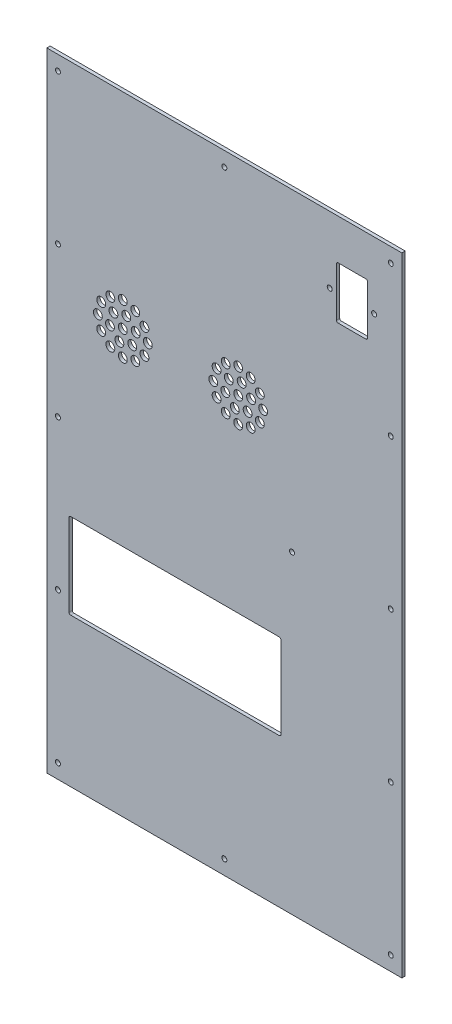
SolidWorks part; units mm, degrees
ref_plane "Спереди" through (0, 0, 0) normal (0, 0, 1) x (1, 0, 0)
ref_plane "Сверху" through (0, 0, 0) normal (0, 1, 0) x (1, 0, 0)
ref_plane "Справа" through (0, 0, 0) normal (1, 0, 0) x (0, 0, -1)
sketch "Эскиз1" plane through (0, 0, 0) normal (0, 0, 1) x (1, 0, 0)
  line L0 (0, 0) -> (320, 0)
  line L1 (0, 0) -> (0, 566)
  line L2 (320, 0) -> (320, 566)
  line L3 (0, 566) -> (320, 566)
  line L4 (10, 553) -> (310, 553) construction
  line L5 (10, 553) -> (10, 13) construction
  line L6 (310, 553) -> (310, 13) construction
  line L7 (10, 13) -> (310, 13) construction
  line L8 (160, 553) -> (160, 13) construction
  circle A0 centre (10, 553) radius 2.25
  circle A1 centre (10, 418) radius 2.25
  circle A2 centre (10, 283) radius 2.25
  circle A3 centre (10, 148) radius 2.25
  circle A4 centre (10, 13) radius 2.25
  circle A5 centre (310, 13) radius 2.25
  circle A6 centre (160, 553) radius 2.25
  circle A7 centre (310, 553) radius 2.25
  circle A8 centre (310, 418) radius 2.25
  circle A9 centre (310, 283) radius 2.25
  circle A10 centre (310, 148) radius 2.25
  circle A11 centre (160, 13) radius 2.25
  dimension "D7" = 4.5
  dimension "D9" = 135
  dimension "D10" = 4.5
  dimension "D12" = 135
  dimension "D13" = 4.5
  dimension "D14" = 4.5
  dimension "D1" = 566
  dimension "D2" = 320
  dimension "D3" = 10
  dimension "D4" = 13
  dimension "D5" = 10
  dimension "D6" = 13
  dimension "D8" = 5
  dimension "D11" = 5
extrude "Бобышка-Вытянуть1" add sketch "Эскиз1" along normal blind 3
sketch "Эскиз2" plane through (0, 0, 0) normal (0, 0, -1) x (-1, 0, 0)
  line L0 (-34.5, 497.8788) -> (-34.5, 452.1212) construction
  line L1 (-50.3712, 513.75) -> (-96.1288, 513.75) construction
  line L2 (-50.3712, 436.25) -> (-96.1288, 436.25) construction
  line L3 (-112, 497.8788) -> (-112, 452.1212) construction
  line L4 (-34.5, 497.8788) -> (-34.5, 452.1212) construction
  line L5 (-50.3712, 513.75) -> (-96.1288, 513.75) construction
  line L6 (-50.3712, 436.25) -> (-96.1288, 436.25) construction
  line L7 (-112, 497.8788) -> (-112, 452.1212) construction
  line L8 (-155.25, 500.5) -> (-124.75, 500.5) construction
  line L9 (-124.75, 475.5) -> (-155.25, 475.5) construction
  line L10 (-155.25, 500.5) -> (-124.75, 500.5) construction
  line L11 (-124.75, 475.5) -> (-155.25, 475.5) construction
  line L16 (-130, 446) -> (-130, 461)
  line L17 (-151, 446) -> (-130, 446)
  line L18 (-151, 461) -> (-151, 446)
  line L19 (-130, 461) -> (-151, 461)
  line L20 (-130, 446) -> (-130, 461) construction
  line L21 (-151, 446) -> (-130, 446) construction
  line L22 (-151, 461) -> (-151, 446) construction
  line L23 (-130, 461) -> (-151, 461) construction
  line L24 (-50.3712, 513.75) -> (-149.75, 513.75)
  line L25 (-149.75, 513.75) -> (-167.5, 496)
  line L26 (-167.5, 496) -> (-167.5, 454)
  line L27 (-157.5, 444) -> (-112.25, 444)
  line L28 (-112.25, 444) -> (-104.5, 436.25)
  line L29 (-104.5, 436.25) -> (-50.3712, 436.25)
  line L30 (-34.5, 452.1212) -> (-34.5, 497.8788)
  line L31 (-167.5, 454) -> (-157.5, 444)
  line L32 (-50.3712, 513.75) -> (-34.5, 497.8788)
  line L33 (-34.5, 452.1212) -> (-50.3712, 436.25)
  arc A0 (-50.3712, 436.25) -> (-34.5, 452.1212) centre (-73.25, 475) ccw construction
  arc A1 (-34.5, 497.8788) -> (-50.3712, 513.75) centre (-73.25, 475) ccw construction
  arc A2 (-112, 452.1212) -> (-96.1288, 436.25) centre (-73.25, 475) ccw construction
  arc A3 (-96.1288, 513.75) -> (-112, 497.8788) centre (-73.25, 475) ccw construction
  arc A4 (-50.3712, 436.25) -> (-34.5, 452.1212) centre (-73.25, 475) ccw construction
  arc A5 (-34.5, 497.8788) -> (-50.3712, 513.75) centre (-73.25, 475) ccw construction
  arc A6 (-112, 452.1212) -> (-96.1288, 436.25) centre (-73.25, 475) ccw construction
  arc A7 (-96.1288, 513.75) -> (-112, 497.8788) centre (-73.25, 475) ccw construction
  arc A8 (-124.75, 475.5) -> (-124.75, 500.5) centre (-127.8878, 488) ccw construction
  arc A9 (-155.25, 500.5) -> (-155.25, 475.5) centre (-152.1122, 488) ccw construction
  arc A10 (-124.75, 475.5) -> (-124.75, 500.5) centre (-127.8878, 488) ccw construction
  arc A11 (-155.25, 500.5) -> (-155.25, 475.5) centre (-152.1122, 488) ccw construction
  circle A12 centre (-164, 511) radius 2.25 construction
  circle A13 centre (-164, 511) radius 2.25 construction
  circle A14 centre (-140.5, 437.5) radius 2.25 construction
  circle A15 centre (-140.5, 437.5) radius 2.25 construction
  circle A16 centre (-26, 447) radius 2.25 construction
  circle A17 centre (-26, 447) radius 2.25 construction
  circle A18 centre (-26, 511) radius 2.25 construction
  circle A19 centre (-26, 511) radius 2.25 construction
  circle A20 centre (-26, 511) radius 2
  circle A21 centre (-26, 447) radius 2
  circle A22 centre (-164, 511) radius 2
  circle A23 centre (-140.5, 437.5) radius 2
  point P35 (-167.5, 444)
  dimension "D8" = 4
  dimension "D9" = 4
  dimension "D10" = 4
  dimension "D11" = 4
  dimension "D2" = 135
  dimension "D3" = 135
  dimension "D4" = 2
  dimension "D5" = 52
  dimension "D6" = 70
  dimension "D7" = 133
  dimension "D12" = 135
  dimension "D13" = 135
  dimension "D1" = 0
sketch "Эскиз3" plane through (0, 0, 0) normal (0, 0, -1) x (-1, 0, 0)
  line L0 (0, 0) -> (-320, 0) construction
  line L1 (0, 566) -> (0, 0) construction
  line L8 (-20, 134) -> (-20, 211)
  line L9 (-211, 134) -> (-20, 134)
  line L10 (-211, 211) -> (-211, 134)
  line L11 (-20, 211) -> (-211, 211)
  dimension "D1" = 211
  dimension "D6" = 77
  dimension "D7" = 20
  dimension "D8" = 191
extrude "Вырез-Вытянуть2" cut sketch "Эскиз3" against normal through all
sketch "Sketch3" plane through (0, 0, 0) normal (0, 0, -1) x (-1, 0, 0)
  line L0 (-20, 173) -> (-182, 173) construction
  line L1 (-20, 173) -> (-182, 173) construction
  line L2 (-202, 23) -> (-202, 543) construction
  line L3 (-202, 23) -> (-202, 543) construction
  line L4 (-221, 312.4311) -> (-221, 163) construction
  line L5 (-101, 153) -> (-101, 178.2817) construction
  line L6 (-211, 211) -> (-211, 134) construction
  line L8 (-20, 134) -> (-20, 211) construction
  line L9 (-202, 283) -> (-221, 283) construction
  circle A0 centre (-101, 163) radius 2.25
  circle A2 centre (-221, 283) radius 2.25
  dimension "D1" = 4.5
  dimension "D7" = 4.5
  dimension "D2" = 10
  dimension "D5" = 81
  dimension "D6" = 10
extrude "Cut-Extrude1" cut sketch "Sketch3" against normal through all
sketch "Эскиз4" plane through (0, 0, 3) normal (0, 0, 1) x (1, 0, 0)
  line L0 (261, 529.5) -> (289, 529.5)
  line L1 (261, 529.5) -> (261, 482.5)
  line L2 (289, 529.5) -> (289, 482.5)
  line L3 (261, 482.5) -> (289, 482.5)
  line L4 (275, 529.5) -> (275, 482.5) construction
  line L5 (261, 506) -> (289, 506) construction
  line L6 (320, 0) -> (320, 566) construction
  line L7 (320, 566) -> (0, 566) construction
  line L8 (255, 506) -> (295, 506) construction
  circle A0 centre (255, 506) radius 2.25
  circle A1 centre (295, 506) radius 2.25
  dimension "D7" = 4.5
  dimension "D1" = 47
  dimension "D2" = 28
  dimension "D3" = 45
  dimension "D4" = 60
  dimension "D5" = 40
  dimension "D6" = 20
extrude "Вырез-Вытянуть3" cut sketch "Эскиз4" against normal through all
fillet "Скругление1" radius 1.5 4 edges at (211, 134, 1.5) (211, 211, 1.5) (20, 134, 1.5) (20, 211, 1.5)
sketch "Эскиз5" plane through (0, 0, 0) normal (0, 0, -1) x (-1, 0, 0)
  line L0 (-172.5, 408.5) -> (-172.5, 353.5) construction
  line L1 (-68.5, 408.5) -> (-68.5, 353.5) construction
  line L2 (-172.5, 381) -> (-188.4099, 365.0901) construction
  line L3 (-68.5, 381) -> (-76.9853, 372.5147) construction
  circle A0 centre (-68.5, 381) radius 27.5 construction
  circle A1 centre (-68.5, 381) radius 27.5 construction
  circle A2 centre (-172.5, 381) radius 27.5 construction
  circle A3 centre (-172.5, 381) radius 27.5 construction
  circle A4 centre (-172.5, 381) radius 12 construction
  circle A5 centre (-172.5, 381) radius 22.5 construction
  circle A6 centre (-172.5, 381) radius 4
  circle A7 centre (-172.5, 358.5) radius 4
  circle A8 centre (-180.9853, 372.5147) radius 4
  circle A9 centre (-183.75, 361.5144) radius 4
  circle A10 centre (-191.9856, 369.75) radius 4
  circle A11 centre (-195, 381) radius 4
  circle A12 centre (-191.9856, 392.25) radius 4
  circle A13 centre (-183.75, 400.4856) radius 4
  circle A14 centre (-172.5, 403.5) radius 4
  circle A15 centre (-161.25, 400.4856) radius 4
  circle A16 centre (-153.0144, 392.25) radius 4
  circle A17 centre (-150, 381) radius 4
  circle A18 centre (-153.0144, 369.75) radius 4
  circle A19 centre (-161.25, 361.5144) radius 4
  circle A20 centre (-184.0911, 384.1058) radius 4
  circle A21 centre (-175.6058, 392.5911) radius 4
  circle A22 centre (-164.0147, 389.4853) radius 4
  circle A23 centre (-160.9089, 377.8942) radius 4
  circle A24 centre (-169.3942, 369.4089) radius 4
  circle A25 centre (-68.5, 381) radius 12 construction
  circle A26 centre (-68.5, 381) radius 22.5 construction
  circle A27 centre (-68.5, 381) radius 4
  circle A28 centre (-68.5, 358.5) radius 4
  circle A29 centre (-76.9853, 372.5147) radius 4
  circle A30 centre (-79.75, 361.5144) radius 4
  circle A31 centre (-87.9856, 369.75) radius 4
  circle A32 centre (-91, 381) radius 4
  circle A33 centre (-87.9856, 392.25) radius 4
  circle A34 centre (-79.75, 400.4856) radius 4
  circle A35 centre (-68.5, 403.5) radius 4
  circle A36 centre (-57.25, 400.4856) radius 4
  circle A37 centre (-49.0144, 392.25) radius 4
  circle A38 centre (-46, 381) radius 4
  circle A39 centre (-49.0144, 369.75) radius 4
  circle A40 centre (-57.25, 361.5144) radius 4
  circle A41 centre (-80.0911, 384.1058) radius 4
  circle A42 centre (-71.6058, 392.5911) radius 4
  circle A43 centre (-60.0147, 389.4853) radius 4
  circle A44 centre (-56.9089, 377.8942) radius 4
  circle A45 centre (-65.3942, 369.4089) radius 4
  point P40 (-172.5, 381)
  point P43 (-172.5, 381)
  point P54 (-172.5, 381)
  point P84 (-68.5, 381)
  point P95 (-68.5, 381)
  dimension "D1" = 45
  dimension "D2" = 24
  dimension "D3" = 8
  dimension "D4" = 45
  dimension "D7" = 45
  dimension "D8" = 24
  dimension "D9" = 8
  dimension "D10" = 45
  dimension "D5" = 12
  dimension "D6" = 6
  dimension "D11" = 12
  dimension "D12" = 6
extrude "Вырез-Вытянуть4" cut sketch "Эскиз5" against normal through all
fillet "Скругление2" radius 1.5 4 edges at (261, 482.5, 1.5) (289, 482.5, 1.5) (289, 529.5, 1.5) (261, 529.5, 1.5)
